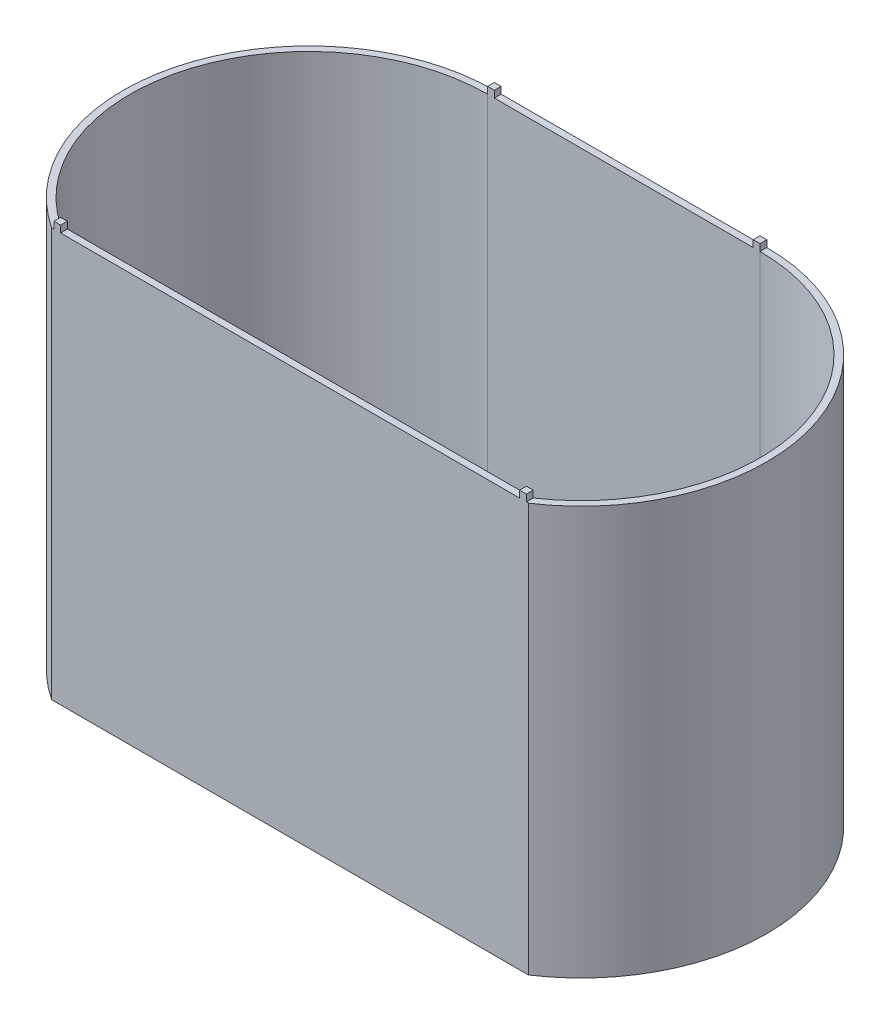
SolidWorks part; units mm, degrees
ref_plane "Front Plane" through (0, 0, 0) normal (0, 0, 1) x (1, 0, 0)
ref_plane "Top Plane" through (0, 0, 0) normal (0, 1, 0) x (1, 0, 0)
ref_plane "Right Plane" through (0, 0, 0) normal (1, 0, 0) x (0, 0, -1)
sketch "Sketch1" plane through (0, 0, 0) normal (0, 1, 0) x (1, 0, 0)
  line L0 (-47.5, 76.871) -> (-77.5, -23.129) construction
  line L1 (-77.5, -23.129) -> (62.5, -23.129)
  line L2 (-7.5, 76.871) -> (-7.5, -23.129) construction
  line L3 (-47.5, 76.871) -> (32.5, 76.871)
  line L4 (32.5, 76.871) -> (62.5, -23.129) construction
  line L5 (-77.5, -23.129) -> (32.5, 76.871) construction
  line L6 (-47.5, 76.871) -> (62.5, -23.129) construction
  arc A1 (-47.5, 76.871) -> (-77.5, -23.129) centre (-47.5, 22.371) ccw
  arc A2 (62.5, -23.129) -> (32.5, 76.871) centre (32.5, 22.371) ccw
  point P0 (-7.5, 40.5074)
  dimension "D3" = 100
  dimension "D1" = 80
  dimension "D2" = 140
extrude "Boss-Extrude2" add sketch "Sketch1" along normal blind 120
shell "Shell2" thickness 2
sketch "Sketch12" plane through (0, 2, 0) normal (0, 1, 0) x (1, 0, 0)
  line L1 (61.8939, -4.0638) -> (49.8939, -4.0638)
  line L2 (61.8939, -4.0638) -> (61.8939, -14.0638)
  line L3 (61.8939, -14.0638) -> (49.8939, -14.0638)
  line L4 (49.8939, -4.0638) -> (49.8939, -14.0638)
  dimension "D1" = 10
  dimension "D2" = 12
  dimension "D3" = 0
extrude "Cut-Extrude4" cut sketch "Sketch12" against normal blind 5
sketch "Sketch16" plane through (-75.4891, 62.8812, 23.129) normal (0, 0, 1) x (0, -1, 0)
  line L0 (-38.2909, 19.7585) -> (25.683, 19.7585) construction
  circle A5 centre (-38.2909, 19.7585) radius 1.58 construction
sketch "Sketch22" plane through (0, 0, 0) normal (0, 1, 0) x (1, 0, 0)
  line L0 (-67.5, -16.629) -> (34.5, -16.629) construction
  line L1 (34.5, -16.629) -> (34.5, 47.3449) construction
  line L2 (-67.5, -1.6489) -> (-67.5, 38.6974) construction
  circle A0 centre (-67.5, -16.629) radius 1.58
  circle A1 centre (-67.5, 47.3449) radius 1.58
  circle A2 centre (-32.5, 26.3449) radius 10
  dimension "D2" = 3.16
  dimension "D3" = 3.16
  dimension "D5" = 20
  dimension "D6" = 35
  dimension "D1" = 63.9739
  dimension "D4" = 10
  dimension "D7" = 21
  dimension "D8" = 102
extrude "Cut-Extrude8" cut sketch "Sketch22" along normal up to next
sketch "Sketch23" plane through (0, 0, 0) normal (0, 1, 0) x (1, 0, 0)
  line L0 (51.8939, 46.6104) -> (51.8939, 0.6104)
  line L1 (51.8939, 0.6104) -> (69.8939, 0.6104)
  line L2 (69.8939, 0.6104) -> (69.8939, 46.6104)
  line L3 (69.8939, 46.6104) -> (71.8939, 46.6104)
  line L4 (71.8939, 46.6104) -> (71.8939, -1.3896)
  line L5 (71.8939, -1.3896) -> (49.8939, -1.3896)
  line L6 (49.8939, -1.3896) -> (49.8939, 46.6104)
  line L7 (49.8939, 46.6104) -> (51.8939, 46.6104)
  dimension "D1" = 46
  dimension "D2" = 2
  dimension "D3" = 2
  dimension "D4" = 2
  dimension "D5" = 46
  dimension "D6" = 0
  dimension "D7" = 18
extrude "Boss-Extrude4" add sketch "Sketch23" along normal offset from surface (30 mm away) 28 up to face at (-32.5, 2, -16.3449) offset beyond the face yes
sketch "Sketch24" plane through (0, 0, 0) normal (0, 1, 0) x (1, 0, 0)
  line L0 (69.8939, 46.6104) -> (71.8939, 46.6104) construction
  line L1 (54.8939, 56.6104) -> (66.8939, 56.6104)
  line L2 (51.8939, 46.6104) -> (51.8939, 41.6104)
  line L3 (51.8939, 41.6104) -> (69.8939, 41.6104)
  line L4 (69.8939, 46.6104) -> (69.8939, 41.6104)
  line L7 (51.8939, 46.6104) -> (49.8939, 46.6104)
  line L8 (49.8939, 51.6104) -> (49.8939, 46.6104)
  line L11 (69.8939, 46.6104) -> (71.8939, 46.6104)
  line L12 (71.8939, 51.6104) -> (71.8939, 46.6104)
  arc A0 (66.8939, 56.6104) -> (71.8939, 51.6104) centre (66.8939, 51.6104) cw
  arc A1 (54.8939, 56.6104) -> (49.8939, 51.6104) centre (54.8939, 51.6104) ccw
  point P17 (71.8939, 56.6104)
  point P20 (49.8939, 56.6104)
  dimension "D4" = 5
  dimension "D1" = 0
  dimension "D2" = 0
  dimension "D3" = 5
  dimension "D5" = 0
  dimension "D6" = 0
  dimension "D7" = 0
  dimension "D8" = 0
extrude "Cut-Extrude9" cut sketch "Sketch24" along normal up to next
sketch "Sketch27" plane through (0, 120, 0) normal (0, 1, 0) x (1, 0, 0)
  line L0 (32.5, 74.871) -> (-47.5, 74.871) construction
  line L1 (-47.5, 76.871) -> (-45.5, 76.871)
  line L2 (-47.5, 76.871) -> (-47.5, 74.871)
  line L3 (-47.5, 74.871) -> (-45.5, 74.871)
  line L4 (-45.5, 76.871) -> (-45.5, 74.871)
  line L6 (-77.5, -23.129) -> (62.5, -23.129) construction
  line L7 (32.5, 76.871) -> (30.5, 76.871)
  line L8 (32.5, 76.871) -> (32.5, 74.871)
  line L9 (32.5, 74.871) -> (30.5, 74.871)
  line L10 (30.5, 76.871) -> (30.5, 74.871)
  line L11 (61.8939, -21.129) -> (59.8939, -21.129)
  line L12 (61.8939, -21.129) -> (61.8939, -23.129)
  line L13 (61.8939, -23.129) -> (59.8939, -23.129)
  line L14 (59.8939, -21.129) -> (59.8939, -23.129)
  line L16 (-76.8939, -21.129) -> (-74.8939, -21.129)
  line L17 (-76.8939, -21.129) -> (-76.8939, -23.129)
  line L18 (-76.8939, -23.129) -> (-74.8939, -23.129)
  line L19 (-74.8939, -21.129) -> (-74.8939, -23.129)
  dimension "D1" = 2
  dimension "D2" = 2
  dimension "D3" = 2
  dimension "D4" = 2
extrude "Boss-Extrude5" add sketch "Sketch27" along normal blind 2
sketch "Sketch3" plane through (0, 180, 0) normal (0, 1, 0) x (1, 0, 0)
  line L0 (-47.5, 76.871) -> (-42.5, 76.871)
  line L1 (-47.5, 76.871) -> (-47.5, 71.871)
  line L2 (-47.5, 71.871) -> (-42.5, 71.871)
  line L3 (-42.5, 76.871) -> (-42.5, 71.871)
  line L4 (32.5, 76.871) -> (27.5, 76.871)
  line L5 (32.5, 76.871) -> (32.5, 71.871)
  line L6 (32.5, 71.871) -> (27.5, 71.871)
  line L7 (27.5, 76.871) -> (27.5, 71.871)
  line L8 (-75.9605, -18.129) -> (-70.9605, -18.129)
  line L9 (-75.9605, -18.129) -> (-75.9605, -23.129)
  line L10 (-75.9605, -23.129) -> (-70.9605, -23.129)
  line L11 (-70.9605, -18.129) -> (-70.9605, -23.129)
  line L12 (60.9605, -18.129) -> (55.9605, -18.129)
  line L13 (60.9605, -18.129) -> (60.9605, -23.129)
  line L14 (60.9605, -23.129) -> (55.9605, -23.129)
  line L15 (55.9605, -18.129) -> (55.9605, -23.129)
  dimension "D1" = 5
  dimension "D2" = 5
  dimension "D3" = 5
  dimension "D4" = 5
  dimension "D5" = 90
  dimension "D6" = 5
  dimension "D7" = 5
  dimension "D8" = 23.4605
  dimension "D9" = 23.4605
  dimension "D10" = 70
  dimension "D11" = 126.921
  dimension "D12" = 100
  dimension "D13" = 100
  dimension "D14" = 5
